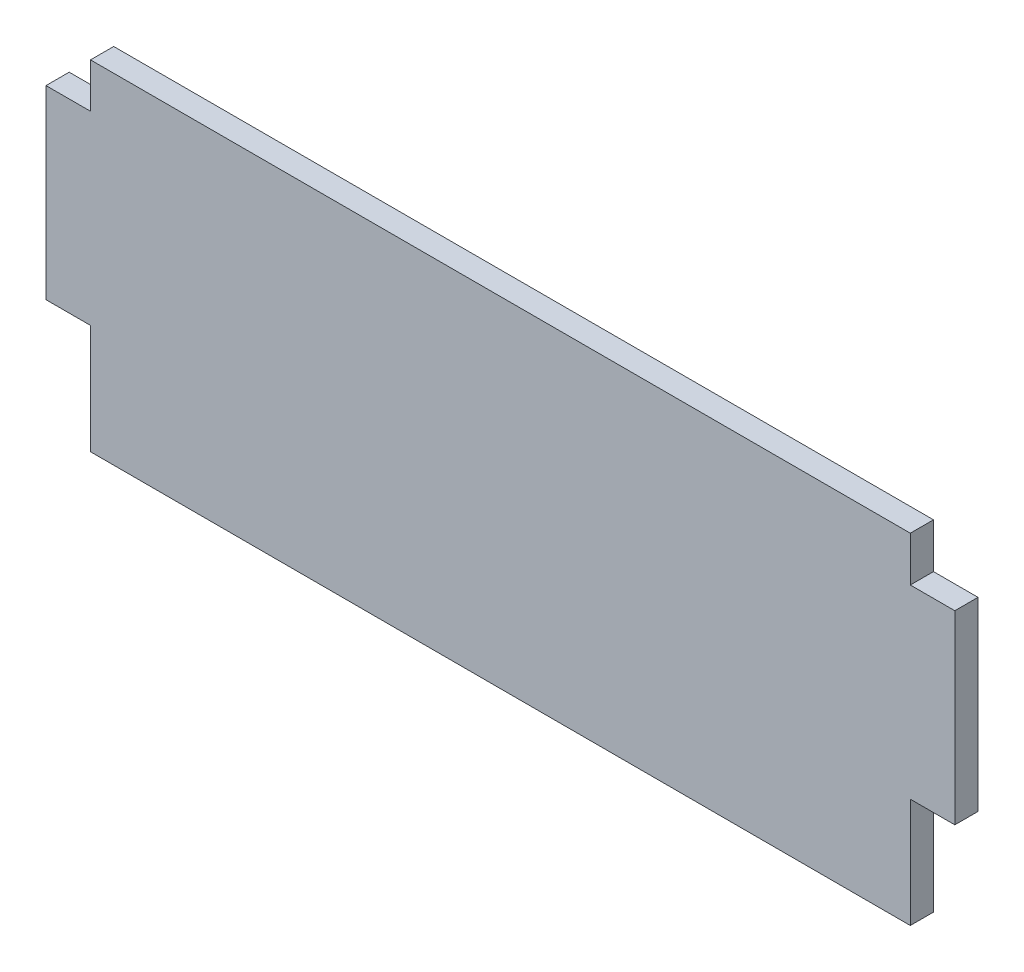
SolidWorks part; units mm, degrees
ref_plane "Front Plane" through (0, 0, 0) normal (0, 0, 1) x (1, 0, 0)
ref_plane "Top Plane" through (0, 0, 0) normal (0, 1, 0) x (1, 0, 0)
ref_plane "Right Plane" through (0, 0, 0) normal (1, 0, 0) x (0, 0, -1)
sketch "Sketch1" plane through (0, 0, 0) normal (0, 0, 1) x (1, 0, 0)
  line L0 (0, 88.011) -> (-3.048, 88.011)
  line L1 (-3.048, 88.011) -> (-3.048, 75.311)
  line L2 (-3.048, 75.311) -> (0, 75.311)
  line L3 (0, 75.311) -> (0, 67.818)
  line L4 (-3.048, 67.818) -> (0, 67.818) construction
  line L5 (0, 67.818) -> (0, 97.155) construction
  line L6 (0, 88.011) -> (0, 91.059)
  line L7 (0, 91.059) -> (56.134, 91.059)
  line L8 (56.134, 91.059) -> (56.134, 87.9856)
  line L9 (56.134, 87.9856) -> (59.182, 87.9856)
  line L10 (59.182, 87.9856) -> (59.182, 75.2856)
  line L11 (59.182, 75.2856) -> (56.134, 75.2856)
  line L12 (56.134, 75.2856) -> (56.134, 67.7926)
  line L13 (56.134, 67.7926) -> (0, 67.818)
  line L14 (56.134, 97.155) -> (56.134, 67.7926) construction
extrude "Boss-Extrude1" add sketch "Sketch1" along normal blind 1.5875
